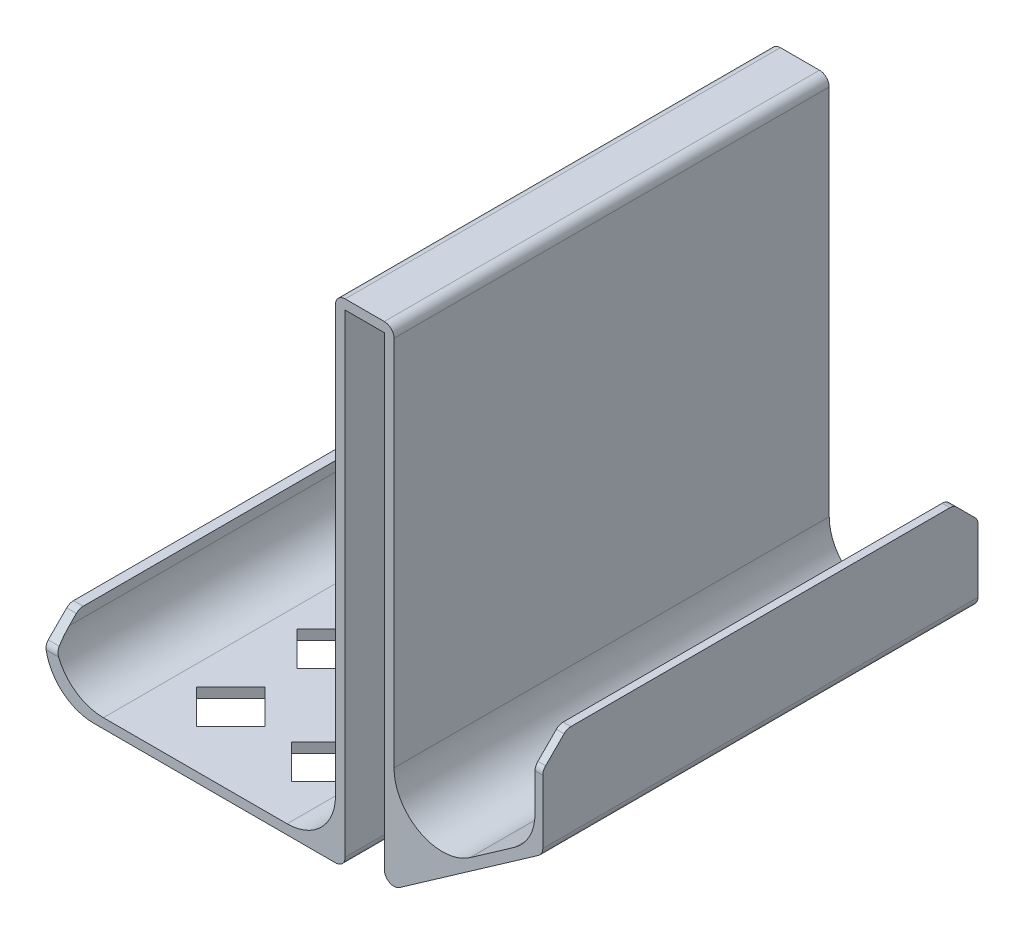
SolidWorks part; units mm, degrees
ref_plane "Plan de face" through (0, 0, 0) normal (0, 0, 1) x (1, 0, 0)
ref_plane "Plan de dessus" through (0, 0, 0) normal (0, 1, 0) x (1, 0, 0)
ref_plane "Plan de droite" through (0, 0, 0) normal (1, 0, 0) x (0, 0, -1)
sketch "Esquisse1" plane through (0, 0, 0) normal (0, 0, 1) x (1, 0, 0)
  line L0 (-4.05, 2.8358) -> (-4.05, 102.8358)
  line L1 (-4.05, 102.8358) -> (4.05, 102.8358)
  line L2 (4.05, 102.8358) -> (4.05, 2.8358)
  line L3 (4.05, 2.8358) -> (36.8161, 25.7789)
  line L4 (36.8161, 25.7789) -> (36.8161, 45.7789)
  line L5 (0, 0) -> (0, 76.9557) construction
  line L6 (-6.05, 4.8358) -> (-6.05, 104.8358)
  line L7 (-6.05, 104.8358) -> (6.05, 104.8358)
  line L8 (6.05, 104.8358) -> (6.05, 6.6778)
  line L9 (6.05, 6.6778) -> (35.2161, 27.1001)
  line L10 (35.2161, 27.1001) -> (35.2161, 45.7789)
  line L11 (35.2161, 45.7789) -> (36.8161, 45.7789)
  line L12 (-6.05, 2.8358) -> (-4.05, 2.8358)
  line L13 (-6.05, 2.8358) -> (-66.05, 2.8358)
  line L14 (-66.05, 2.8358) -> (-66.05, 16.889)
  line L15 (-66.05, 16.889) -> (-64.05, 16.889)
  line L16 (-64.05, 16.889) -> (-64.05, 4.8358)
  line L17 (-64.05, 4.8358) -> (-6.05, 4.8358)
  point P10 (0, 102.8358)
  dimension "D1" = 8.1
  dimension "D2" = 100
  dimension "D3" = 55
  dimension "D4" = 40
  dimension "D5" = 20
  dimension "D6" = 2
  dimension "D7" = 1.6
  dimension "D8" = 2
  dimension "D9" = 2
  dimension "D10" = 100
  dimension "D11" = 2
  dimension "D12" = 2
  dimension "D13" = 2
  dimension "D14" = 60
extrude "Boss.-Extru.1" add sketch "Esquisse1" along normal blind 90
fillet "Congé1" radius 10 5 edges at (35.2161, 27.1001, 45) (6.05, 6.6778, 45) (-64.05, 4.8358, 45) (-6.05, 4.8358, 45) (-66.05, 2.8358, 45)
chamfer "Chanfrein1" distance 5 angle 45 4 edges at (36.0161, 45.7789, 0) (36.0161, 45.7789, 90) (-65.05, 16.889, 0) (-65.05, 16.889, 90)
fillet "Congé2" radius 2 13 edges at (36.8161, 25.7789, 45) (4.05, 2.8358, 45) (36.0161, 40.7789, 90) (36.0161, 40.7789, 0) (36.0161, 45.7789, 5) (36.0161, 45.7789, 85) (-64.8055, 11.889, 90) (-65.05, 16.889, 85) (-64.8055, 11.889, 0) (-65.05, 16.889, 5) (6.05, 104.8358, 45) (-6.05, 104.8358, 45) (-4.05, 2.8358, 45)
sketch "Esquisse2" plane through (0, 2.8358, 0) normal (0, -1, 0) x (1, 0, 0)
  line L0 (-49.8835, 12.4428) -> (-42.8124, 19.5139)
  line L1 (-49.8835, 12.4428) -> (-42.8124, 5.3717)
  line L2 (-42.8124, 19.5139) -> (-35.7414, 12.4428)
  line L3 (-42.8124, 5.3717) -> (-35.7414, 12.4428)
  line L4 (-56.05, 90) -> (-56.05, 0) construction
  point P6 (-41.0447, 3.604)
  dimension "D1" = 45
  dimension "D2" = 10
extrude "Enlèv. mat.-Extru.1" cut sketch "Esquisse2" against normal up to next (2 mm away)
pattern_linear "Répétition linéaire1" count 4 spacing 20.8287 along (0, 0, 1) count 2 spacing 19.6914 along (1, 0, 0) of "Enlèv. mat.-Extru.1"
